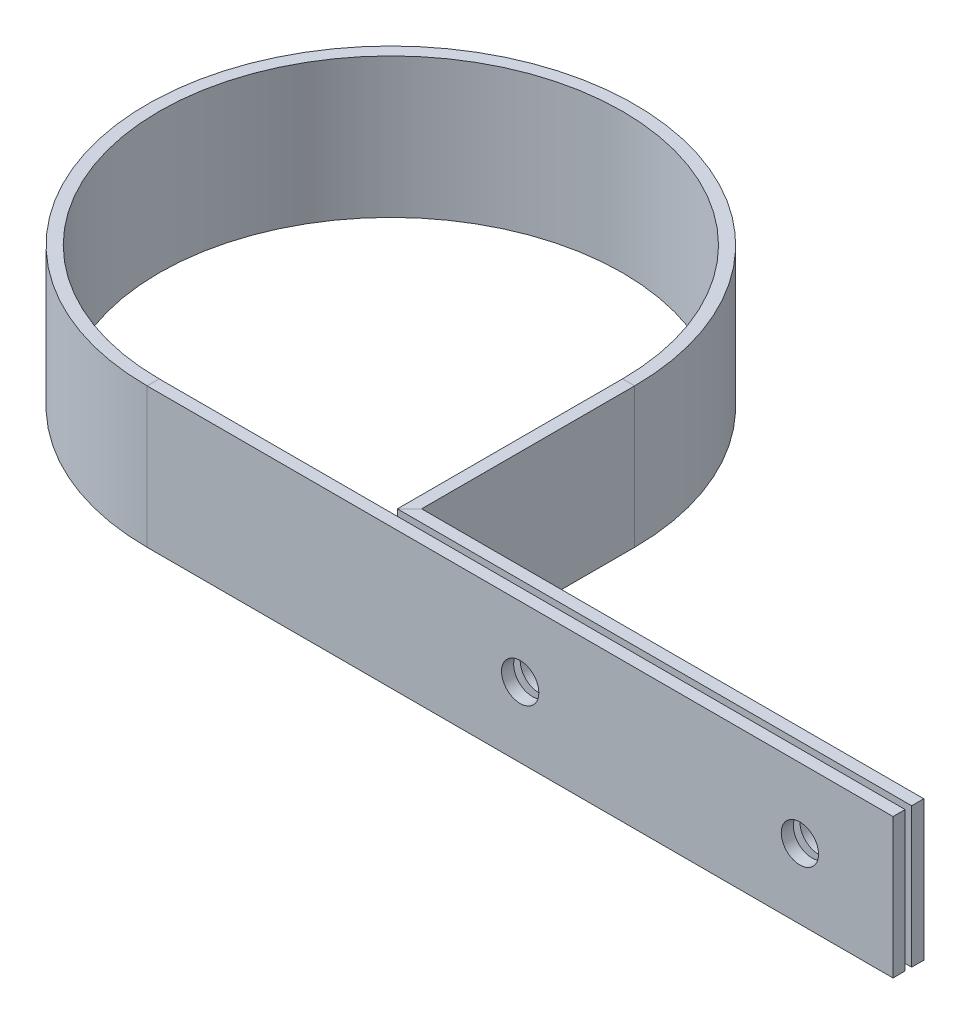
SolidWorks part; units mm, degrees
ref_plane "Front" through (0, 0, 0) normal (0, 0, 1) x (1, 0, 0)
ref_plane "Top" through (0, 0, 0) normal (0, 1, 0) x (1, 0, 0)
ref_plane "Right" through (0, 0, 0) normal (1, 0, 0) x (0, 0, -1)
sketch "Sketch1" plane through (0, 0, 0) normal (0, 1, 0) x (1, 0, 0)
  line L0 (0, 0) -> (-101.6, 0)
  line L1 (0, 2.54) -> (-69.2258, 2.54)
  line L2 (-69.2258, 32.385) -> (-69.2258, 2.54)
  line L3 (0, 2.54) -> (-101.6, 2.54) construction
  arc A1 (-69.2258, 32.385) -> (-101.6, 0) centre (-101.6108, 32.385) ccw
  point P8 (0, 0)
  point P10 (0, 0)
  point P11 (-69.2258, -4.2011)
  dimension "D2" = 64.77
  dimension "D1" = 101.6
  dimension "D5" = 101.6
  dimension "D3" = 2.54
sketch "Sketch2" plane through (0, 0, 0) normal (1, 0, 0) x (0, 0, -1)
  line L1 (0.8255, -9.525) -> (-0.8255, -9.525)
  line L2 (0.8255, -9.525) -> (0.8255, 9.525)
  line L3 (0.8255, 9.525) -> (-0.8255, 9.525)
  line L4 (-0.8255, -9.525) -> (-0.8255, 9.525)
  line L5 (0.8255, -9.525) -> (-0.8255, 9.525) construction
  line L6 (0.8255, 9.525) -> (-0.8255, -9.525) construction
  point P0 (0, 0)
  dimension "D1" = 19.05
  dimension "D2" = 1.651
sweep "Sweep1" add profiles "Sketch2" path "Sketch1"
sketch "Sketch3" plane through (0, 0, -3.3655) normal (0, 0, -1) x (-1, 0, 0)
  line L0 (66.04, 0) -> (50.7874, 0) construction
  line L1 (66.04, 9.525) -> (66.04, -9.525) construction
  line L2 (50.7874, 0) -> (12.6874, 0) construction
  circle A0 centre (50.7874, 0) radius 5.334 construction
  circle A1 centre (50.7874, 0) radius 2.54
  circle A2 centre (12.6874, 0) radius 2.54
  dimension "D1" = 10.668
  dimension "D2" = 5.08
  dimension "D4" = 5.08
  dimension "D3" = 38.1
extrude "Cut-Extrude1" cut sketch "Sketch3" against normal through all
sketch "Sketch4" plane through (0, 0, -3.3655) normal (0, 0, -1) x (-1, 0, 0)
  line L0 (50.7874, 0) -> (12.6874, 0) construction
  dimension "D1" = 38.1
